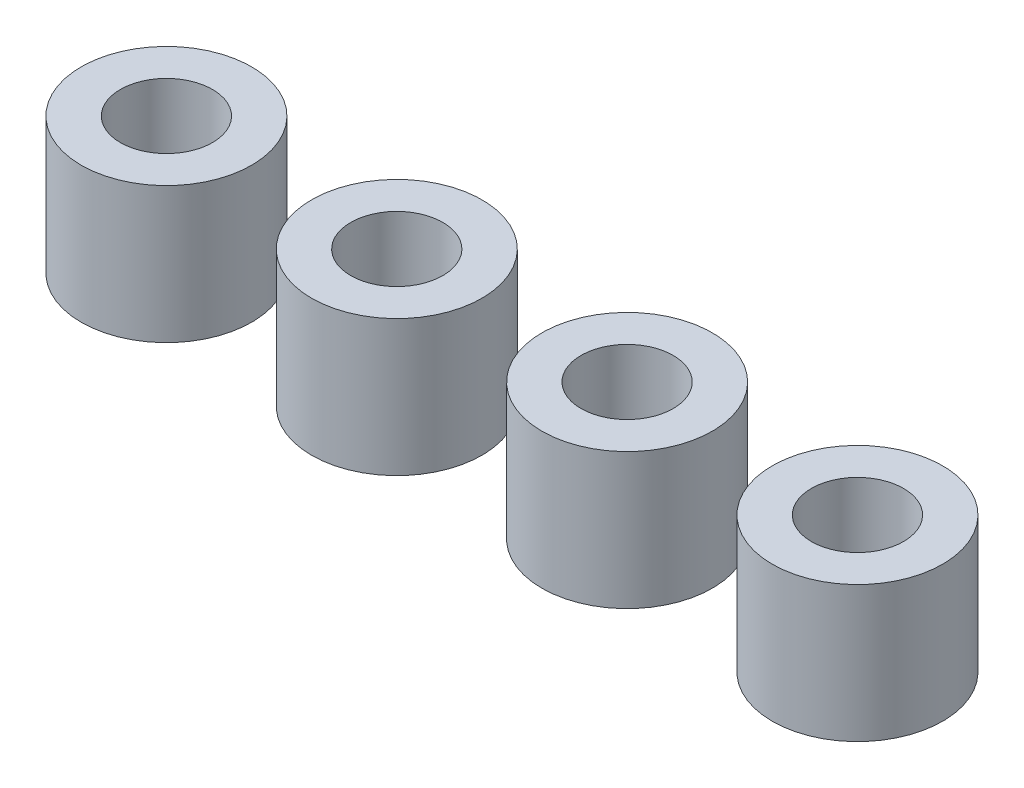
SolidWorks part; units mm, degrees
material "Pure Gold"
ref_plane "Front Plane" through (0, 0, 0) normal (0, 0, 1) x (1, 0, 0)
ref_plane "Top Plane" through (0, 0, 0) normal (0, 1, 0) x (1, 0, 0)
ref_plane "Right Plane" through (0, 0, 0) normal (1, 0, 0) x (0, 0, -1)
sketch "Sketch1" plane through (0, 0, 0) normal (0, 1, 0) x (1, 0, 0)
  circle A0 centre (-2.8151, 1.6815) radius 0.94
  circle A1 centre (-2.8151, 1.6815) radius 0.508
  circle A2 centre (-0.2751, 1.6815) radius 0.94
  circle A3 centre (-0.2751, 1.6815) radius 0.508
  circle A4 centre (2.2649, 1.6815) radius 0.94
  circle A5 centre (2.2649, 1.6815) radius 0.508
  circle A6 centre (4.8049, 1.6815) radius 0.94
  circle A7 centre (4.8049, 1.6815) radius 0.508
  dimension "D1" = 1.88
  dimension "D2" = 1.016
extrude "Boss-Extrude1" add sketch "Sketch1" along normal blind 1.5
